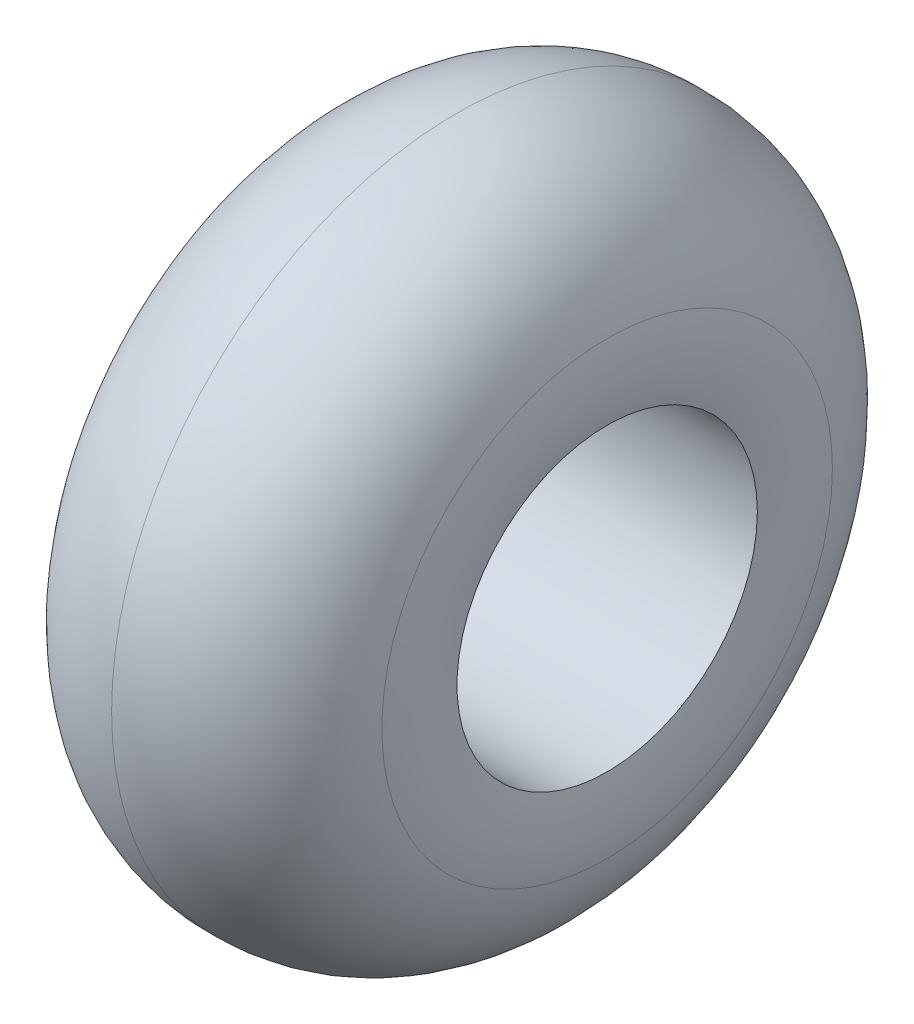
SolidWorks part; units mm, degrees
ref_plane "Front Plane" through (0, 0, 0) normal (0, 0, 1) x (1, 0, 0)
ref_plane "Top Plane" through (0, 0, 0) normal (0, 1, 0) x (1, 0, 0)
ref_plane "Right Plane" through (0, 0, 0) normal (1, 0, 0) x (0, 0, -1)
sketch "Sketch2" plane through (0, 0, 0) normal (0, 0, 1) x (1, 0, 0)
  line L0 (0, 63.5) -> (0, 146.05)
  line L1 (-63.5, 63.5) -> (63.5, 63.5)
  line L2 (0, 0) -> (-84.0428, 0) construction
  arc A4 (0, 146.05) -> (63.5, 95.25) centre (1.2803, 82.5629) cw
  arc A5 (63.5, 95.25) -> (63.5, 63.5) centre (-11.028, 79.375) cw
  arc A6 (0, 146.05) -> (-63.5, 95.25) centre (-1.2803, 82.5629) ccw
  arc A7 (-63.5, 95.25) -> (-63.5, 63.5) centre (11.028, 79.375) ccw
  point P15 (-0.8707, 149.6427)
  point P16 (-62.9253, 107.204)
  dimension "D4" = 63.5
  dimension "D5" = 127
  dimension "D6" = 63.5
  dimension "D7" = 63.5
  dimension "D8" = 63.5
  dimension "D9" = 76.2
  dimension "D10" = 76.2
  dimension "D1" = 63.5
  dimension "D2" = 127
  dimension "D3" = 82.55
  dimension "D11" = 50.8
  dimension "D12" = 50.8
revolve "Revolve1" add sketch "Sketch2" angle 360 about L2
